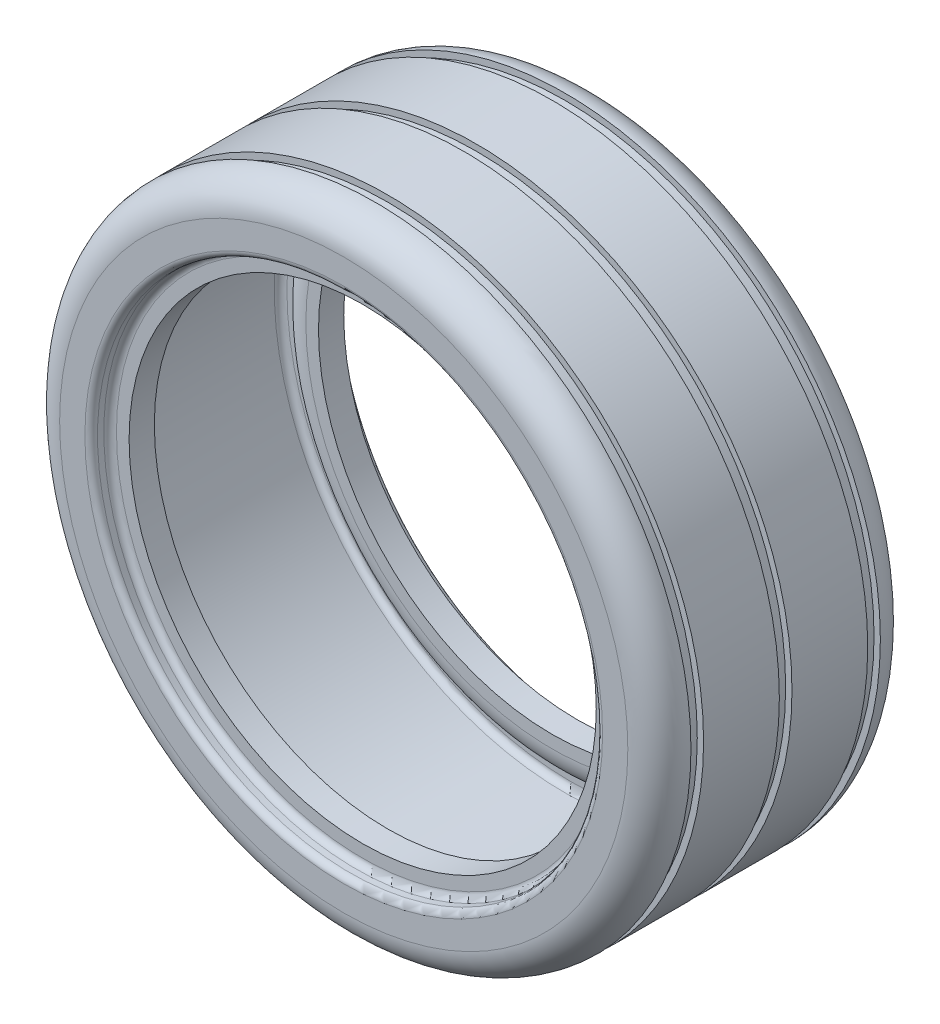
SolidWorks part; units mm, degrees
material "Silicon Rubber"
ref_plane "Front Plane" through (0, 0, 0) normal (0, 0, 1) x (1, 0, 0)
ref_plane "Top Plane" through (0, 0, 0) normal (0, 1, 0) x (1, 0, 0)
ref_plane "Right Plane" through (0, 0, 0) normal (1, 0, 0) x (0, 0, -1)
sketch "Sketch1" plane through (0, 0, 0) normal (1, 0, 0) x (0, 0, -1)
  line L0 (0, 0) -> (0, 160) construction
  line L7 (0, 80) -> (40, 80) construction
  line L8 (0, 160) -> (40, 160) construction
  line L10 (0, 160) -> (0, 180) construction
  line L16 (0, 180) -> (30, 180)
  line L17 (40, 170) -> (40, 162)
  line L18 (38, 160) -> (36, 160)
  line L24 (34, 158) -> (34, 154)
  line L25 (0, 172) -> (30, 172)
  line L26 (32, 170) -> (32, 167.1652)
  line L27 (32, 167.1652) -> (32, 167.1652)
  line L28 (26, 158) -> (26, 154)
  line L29 (34, 154) -> (26, 154)
  line L30 (-26, 158) -> (-26, 154)
  line L31 (-34, 154) -> (-26, 154)
  line L32 (-34, 158) -> (-34, 154)
  line L33 (-38, 160) -> (-36, 160)
  line L34 (-40, 170) -> (-40, 162)
  line L35 (-32, 170) -> (-32, 167.1652)
  line L36 (0, 172) -> (-30, 172)
  line L37 (0, 180) -> (-30, 180)
  arc A4 (38, 160) -> (40, 162) centre (38, 162) ccw
  arc A5 (36, 160) -> (34, 158) centre (36, 158) ccw
  arc A6 (30, 180) -> (40, 170) centre (30, 170) cw
  arc A7 (30, 172) -> (32, 170) centre (30, 170) cw
  arc A8 (32, 167.1652) -> (32, 167.1652) centre (32, 167.1652) ccw
  arc A9 (32, 167.1652) -> (26, 158) centre (36, 158) ccw
  arc A10 (-36, 160) -> (-34, 158) centre (-36, 158) cw
  arc A11 (-38, 160) -> (-40, 162) centre (-38, 162) cw
  arc A12 (-32, 167.1652) -> (-26, 158) centre (-36, 158) cw
  arc A13 (-30, 172) -> (-32, 170) centre (-30, 170) ccw
  arc A14 (-30, 180) -> (-40, 170) centre (-30, 170) ccw
  point P15 (34, 160)
  dimension "D3" = 20
  dimension "D6" = 2
  dimension "D7" = 10
  dimension "D1" = 160
  dimension "D2" = 40
  dimension "D4" = 6
  dimension "D5" = 6
  dimension "D8" = 8
revolve "Revolve1" add sketch "Sketch1" angle 360 about L7
sketch "Sketch2" plane through (0, 0, 0) normal (1, 0, 0) x (0, 0, -1)
  line L0 (30, 180) -> (30, -20) construction
  line L1 (26, 204.364) -> (30, 204.364)
  line L2 (26, 204.364) -> (26, 178)
  line L3 (26, 178) -> (30, 178)
  line L4 (30, 204.364) -> (30, 178)
  line L5 (30, 180) -> (-30, 180) construction
  line L6 (0, 180) -> (0, 217.5742) construction
  line L7 (-26, 178) -> (-30, 178)
  line L8 (-30, 204.364) -> (-30, 178)
  line L9 (-26, 204.364) -> (-30, 204.364)
  line L10 (-26, 204.364) -> (-26, 178)
  line L12 (-2, 204.364) -> (2, 204.364)
  line L13 (-2, 204.364) -> (-2, 178)
  line L14 (-2, 178) -> (2, 178)
  line L15 (2, 204.364) -> (2, 178)
  dimension "D1" = 4
  dimension "D2" = 2
  dimension "D3" = 2
  dimension "D4" = 4
  dimension "D5" = 2
ref_axis "Axis1" through (0, 80, -30) along (0, 0, 1)
revolve "Cut-Revolve1" cut sketch "Sketch2" angle 360 about axis through (0, 80, -30) along (0, 0, 1)
scale "Scale1" scale about centroid uniform scaling yes scale factor 0.5
